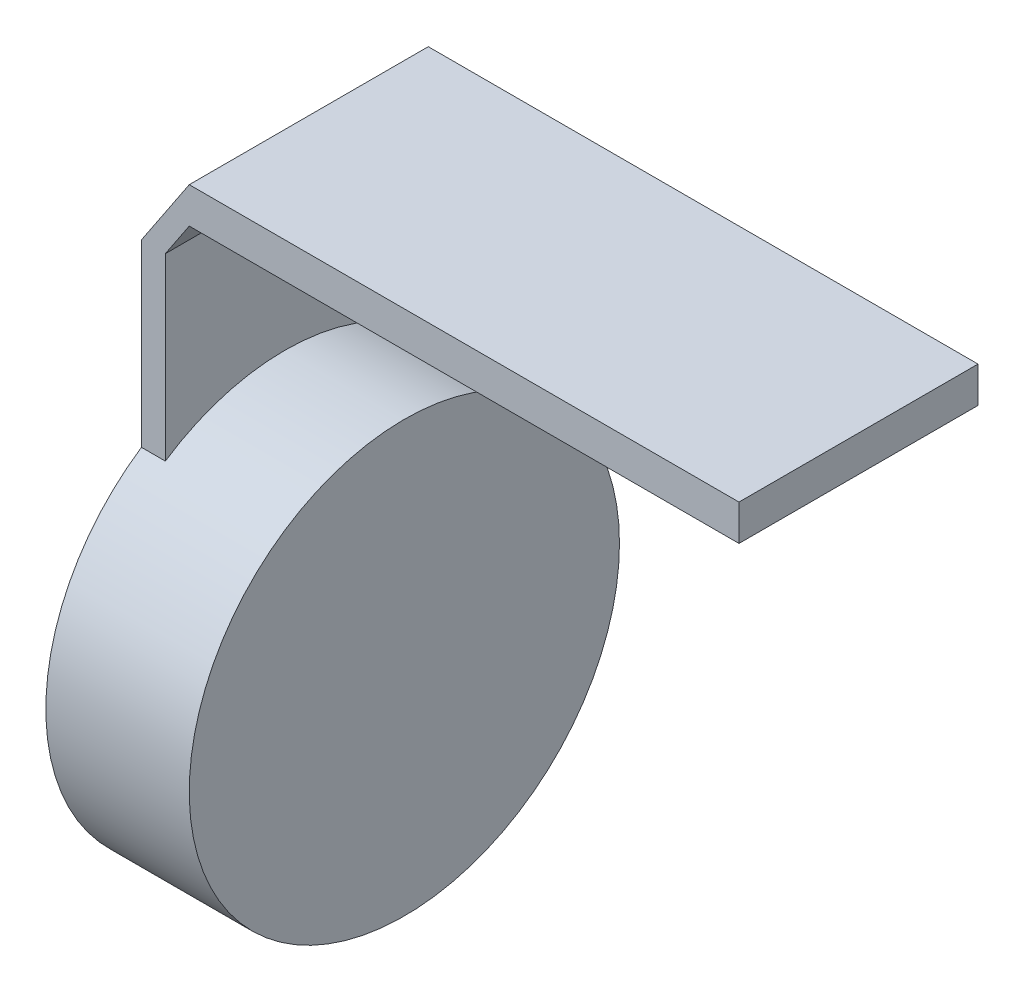
SolidWorks part; units mm, degrees
ref_plane "Front Plane" through (0, 0, 0) normal (0, 0, 1) x (1, 0, 0)
ref_plane "Top Plane" through (0, 0, 0) normal (0, 1, 0) x (1, 0, 0)
ref_plane "Right Plane" through (0, 0, 0) normal (1, 0, 0) x (0, 0, -1)
sketch "Sketch1" plane through (0, 0, 0) normal (1, 0, 0) x (0, 0, -1)
  circle A1 centre (0, 0) radius 18
extrude "Boss-Extrude1" add sketch "Sketch1" along normal blind 10
sketch "Sketch2" plane through (0, 0, 0) normal (-1, 0, 0) x (0, 0, 1)
  line L0 (-10, 14.9666) -> (-10, 30)
  line L3 (-10, 30) -> (10, 30)
  line L5 (0, 0) -> (10, 30) construction
  line L6 (-10, 30) -> (0, 0) construction
  line L7 (10, 14.9666) -> (10, 30)
  arc A0 (-10, 14.9666) -> (10, 14.9666) centre (0, 0) ccw
  dimension "D1" = 30
extrude "Boss-Extrude2" add sketch "Sketch2" along normal blind 2
sketch "Sketch5" plane through (0, 0, -10) normal (0, 0, -1) x (-1, 0, 0)
  line L2 (-2, 36) -> (-48, 36)
  line L3 (-2, 33) -> (-48, 33)
  line L4 (-48, 33) -> (-48, 36)
  line L5 (-2, 33) -> (0, 30)
  line L6 (2, 30) -> (-2, 36)
  line L9 (0, 30) -> (0, 14.9666)
  line L10 (0, 14.9666) -> (2, 14.9666)
  line L11 (2, 14.9666) -> (2, 30)
  line L12 (2, 30) -> (0, 30)
  line L13 (0, 30) -> (0, 14.9666)
  line L14 (0, 14.9666) -> (2, 14.9666)
  line L15 (2, 14.9666) -> (2, 30)
  dimension "D1" = 3
  dimension "D3" = 3
  dimension "D2" = 0
extrude "Boss-Extrude4" add sketch "Sketch5" against normal blind 20
